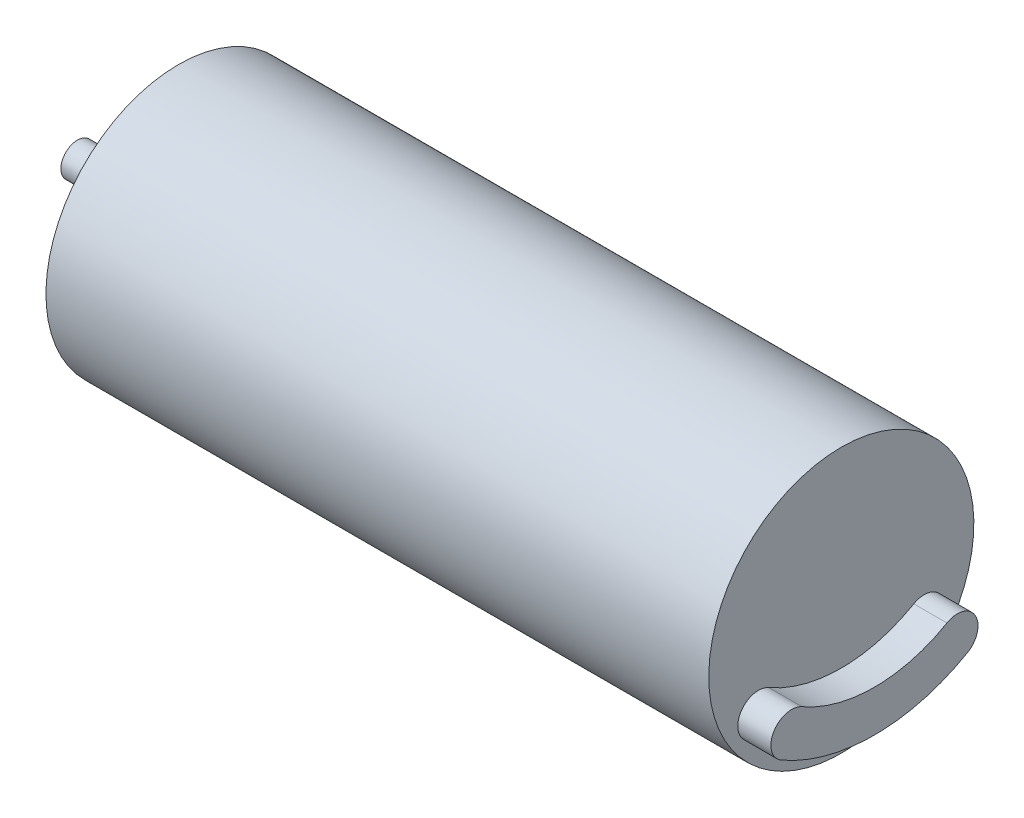
SolidWorks part; units mm, degrees
ref_plane "Front Plane" through (0, 0, 0) normal (0, 0, 1) x (1, 0, 0)
ref_plane "Top Plane" through (0, 0, 0) normal (0, 1, 0) x (1, 0, 0)
ref_plane "Right Plane" through (0, 0, 0) normal (1, 0, 0) x (0, 0, -1)
sketch "Sketch9" plane through (0, 0, 0) normal (0, 0, 1) x (1, 0, 0)
  line L0 (-23.05, 1) -> (-23.05, 0)
  line L1 (-23.05, 0) -> (-17.95, 0)
  line L2 (-17.95, 0) -> (-17.95, 1)
  line L3 (-17.95, 1) -> (-23.05, 1)
  line L4 (-23.05, 0) -> (-17.95, 0) construction
revolve "Revolve2" add sketch "Sketch9" angle 360 about L1
sketch "Sketch11" plane through (0, 0, 0) normal (0, 0, 1) x (1, 0, 0)
  line L0 (-16.95, 8) -> (-16.95, 0)
  line L1 (-16.95, 0) -> (23.05, 0)
  line L2 (23.05, 0) -> (23.05, 8)
  line L3 (23.05, 8) -> (-16.95, 8)
  line L4 (-16.95, 0) -> (23.05, 0) construction
revolve "Revolve3" add sketch "Sketch11" angle 360 about L1
ref_plane "Plane1" through (23.05, 0, 0) normal (1, 0, 0) x (0, 0, -1)
sketch "Sketch15" plane through (23.05, 0, 0) normal (1, 0, 0) x (0, 0, -1)
  arc A0 (4.375, -2.3777) -> (5.625, -4.5428) centre (5, -3.4603) cw
  arc A1 (5.625, -4.5428) -> (-5.625, -4.5428) centre (0, 5.2) cw
  arc A2 (-5.625, -4.5428) -> (-4.375, -2.3777) centre (-5, -3.4603) cw
  arc A3 (-4.375, -2.3777) -> (4.375, -2.3777) centre (0, 5.2) ccw
extrude "Boss-Extrude3" add sketch "Sketch15" along normal blind 2
ref_plane "Plane2" through (-16.95, 0, 0) normal (-1, 0, 0) x (0, 0, 1)
sketch "Sketch20" plane through (-16.95, 0, 0) normal (-1, 0, 0) x (0, 0, 1)
  circle A0 centre (0, 0) radius 4.5
extrude "Boss-Extrude4" add sketch "Sketch20" along normal blind 1
hole_wizard "Ø7.0 (7) Diameter Hole2" positions "Sketch22" profile "Sketch21" hole size "Ø7.0" standard "ANSI Metric"
sketch "Sketch22" plane through (-17.95, 0, 0) normal (1, 0, 0) x (0, 0, -1)
  point P0 (0, 0)
sketch "Sketch21" plane through (-17.95, 0, 0) normal (0, 1, 0) x (0, 0, -1)
  line L0 (0, 0) -> (0, 0.5)
  line L1 (0, 0.5) -> (3.5, 0.5)
  line L2 (3.5, 0.5) -> (3.5, 0)
  line L5 (3.5, 0) -> (0, 0)
  line L10 (0, 0.5) -> (-3.5, 0.5) construction
  line L11 (0, -6.35) -> (0, 107.95) construction
  dimension "Hole Dia." = 7
  dimension "Hole Depth" = 0.5
  dimension "Drill Angle" = 180
hole_wizard "Hole2" positions "Sketch24" profile "Sketch23" legacy
sketch "Sketch24" plane through (-16.95, 0, 0) normal (-1, 0, 0) x (0, 0, 1)
  point P0 (-4.7631, -2.75)
  point P1 (4.7631, -2.75)
  point P2 (0, 5.5)
sketch "Sketch23" plane through (-16.95, -2.75, -4.7631) normal (0, 1, 0) x (0, 0, 1)
  line L0 (0, 0) -> (0, 3.5)
  line L1 (0, 3.5) -> (0.7835, 3.5)
  line L2 (0.7835, 3.5) -> (0.7835, 0)
  line L3 (0.7835, 0) -> (0, 0)
  line L4 (0, 110) -> (0, -10) construction
  dimension "Diameter" = 1.567
  dimension "Depth" = 3.5
